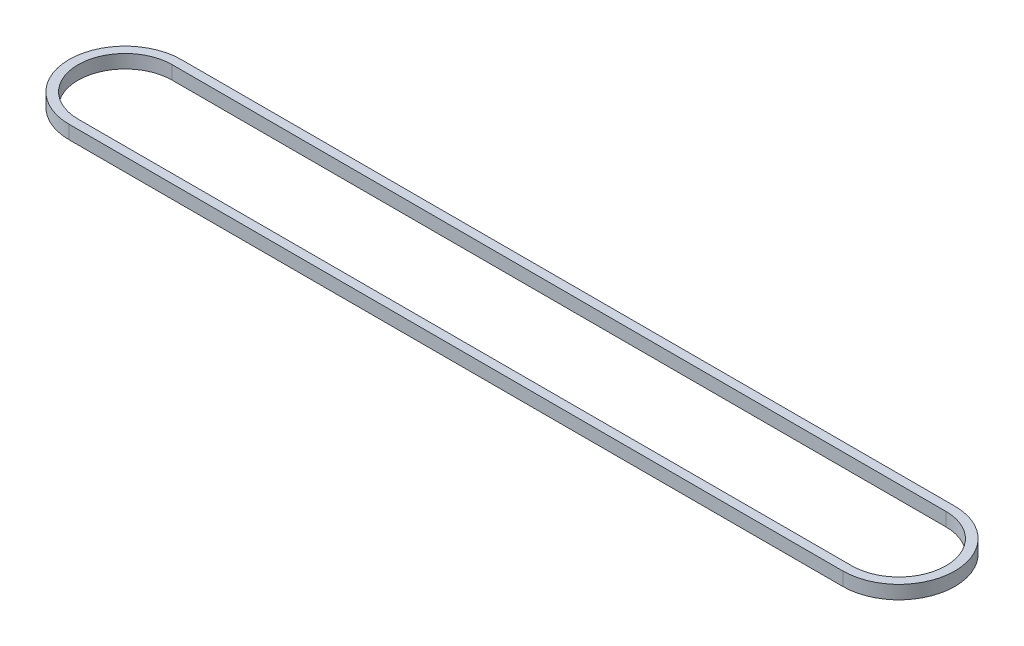
SolidWorks part; units mm, degrees
ref_plane "Front Plane" through (0, 0, 0) normal (0, 0, 1) x (1, 0, 0)
ref_plane "Top Plane" through (0, 0, 0) normal (0, 1, 0) x (1, 0, 0)
ref_plane "Right Plane" through (0, 0, 0) normal (1, 0, 0) x (0, 0, -1)
sketch "Sketch1" plane through (0, 0, 0) normal (0, 1, 0) x (1, 0, 0)
  line L0 (-32.6689, 12.5) -> (139.8311, 12.5)
  line L1 (-32.6689, -12.5) -> (139.8311, -12.5)
  line L2 (-32.6689, 10.5) -> (139.8311, 10.5)
  line L3 (-32.6689, -10.5) -> (139.8311, -10.5)
  arc A0 (-32.6689, 12.5) -> (-32.6689, -12.5) centre (-32.6689, 0) ccw
  arc A1 (139.8311, -12.5) -> (139.8311, 12.5) centre (139.8311, 0) ccw
  arc A2 (139.8311, -10.5) -> (139.8311, 10.5) centre (139.8311, 0) ccw
  arc A3 (-32.6689, 10.5) -> (-32.6689, -10.5) centre (-32.6689, 0) ccw
  dimension "D1" = 25
  dimension "D2" = 2
  dimension "D3" = 172.5
extrude "Boss-Extrude1" add sketch "Sketch1" along normal blind 3
